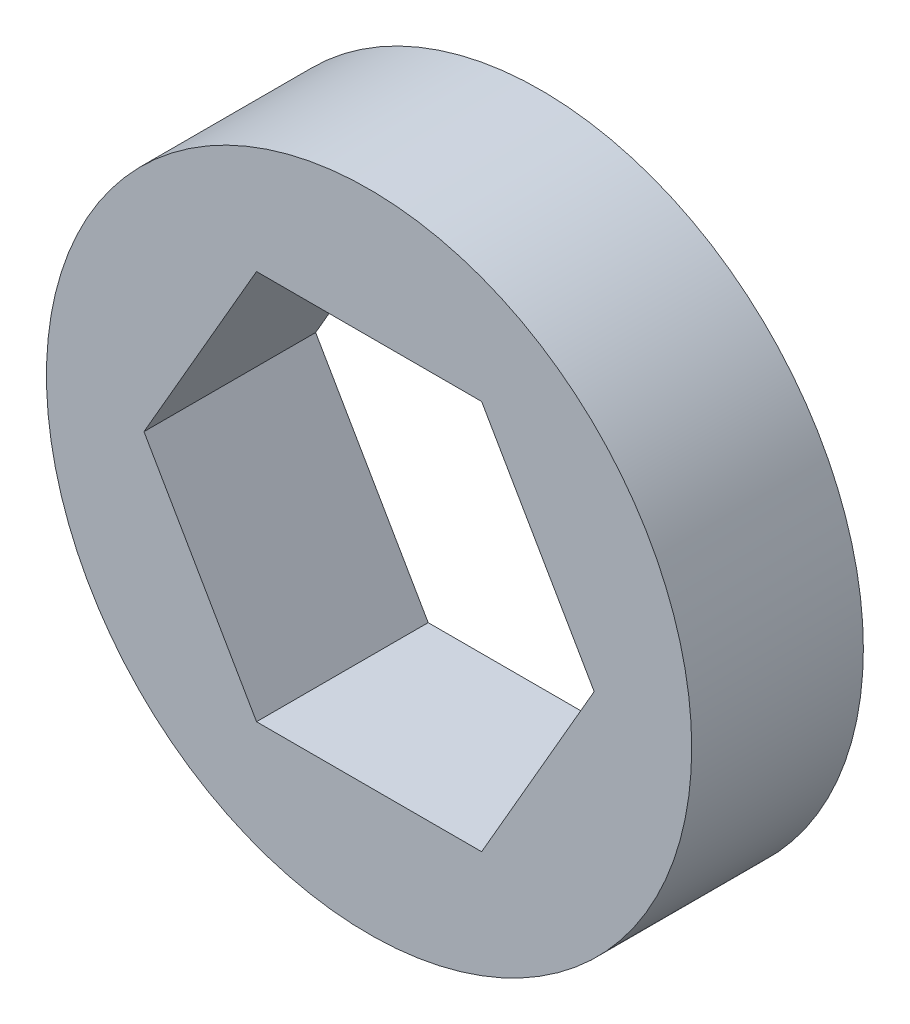
SolidWorks part; units mm, degrees
ref_plane "Front Plane" through (0, 0, 0) normal (0, 0, 1) x (1, 0, 0)
ref_plane "Top Plane" through (0, 0, 0) normal (0, 1, 0) x (1, 0, 0)
ref_plane "Right Plane" through (0, 0, 0) normal (1, 0, 0) x (0, 0, -1)
sketch "Sketch1" plane through (0, 0, 0) normal (0, 0, 1) x (1, 0, 0)
  line L1 (-7.3279, 0) -> (-3.6639, -6.3461)
  line L2 (-3.6639, -6.3461) -> (3.664, -6.3461)
  line L3 (3.664, -6.3461) -> (7.3279, 0)
  line L4 (7.3279, 0) -> (3.6639, 6.3461)
  line L5 (3.6639, 6.3461) -> (-3.664, 6.3461)
  line L6 (-3.664, 6.3461) -> (-7.3279, 0)
  circle A0 centre (0, 0) radius 10.5029
  circle A1 centre (0, 0) radius 7.3279 construction
  circle A2 centre (0, 0) radius 6.3461 construction
  dimension "D1" = 14.6558
  dimension "D2" = 21.0058
extrude "Boss-Extrude1" add sketch "Sketch1" along normal blind 5.588
